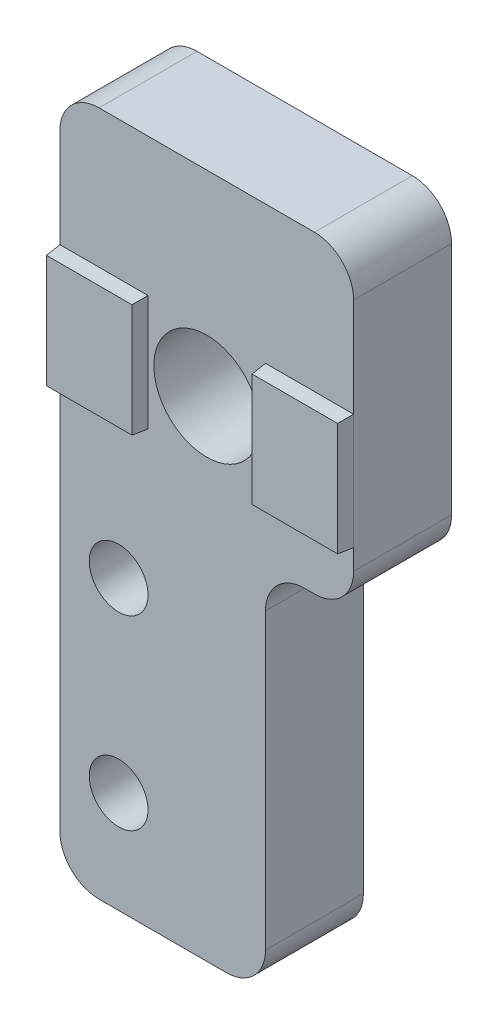
SolidWorks part; units mm, degrees
material "ABS"
ref_plane "Front Plane" through (0, 0, 0) normal (0, 0, 1) x (1, 0, 0)
ref_plane "Top Plane" through (0, 0, 0) normal (0, 1, 0) x (1, 0, 0)
ref_plane "Right Plane" through (0, 0, 0) normal (1, 0, 0) x (0, 0, -1)
sketch "Sketch1" plane through (0, 0, 0) normal (0, 0, 1) x (1, 0, 0)
  line L0 (0, -2) -> (0, -33)
  line L1 (2, 0) -> (13, 0)
  line L2 (2, -35) -> (8.5, -35)
  line L3 (15, -2) -> (15, -14)
  line L6 (7.5, 20) -> (7.5, -35) construction
  line L10 (13, -16) -> (12.5, -16)
  line L11 (10.5, -33) -> (10.5, -18)
  circle A0 centre (7.5, -10) radius 2.7
  circle A1 centre (3, -29.8) radius 1.5
  circle A2 centre (3, -20.3) radius 1.5
  arc A3 (10.5, -33) -> (8.5, -35) centre (8.5, -33) cw
  arc A4 (2, -35) -> (0, -33) centre (2, -33) cw
  arc A5 (0, -2) -> (2, 0) centre (2, -2) cw
  arc A6 (13, 0) -> (15, -2) centre (13, -2) cw
  arc A7 (15, -14) -> (13, -16) centre (13, -14) cw
  arc A8 (12.5, -16) -> (10.5, -18) centre (12.5, -18) ccw
  point P1 (0, 0)
  point P20 (0, -35)
  point P23 (0, 0)
  point P26 (15, 0)
  dimension "D3" = 5.4
  dimension "D4" = 10
  dimension "D5" = 9.5
  dimension "D6" = 5.2
  dimension "D7" = 3
  dimension "D8" = 3
  dimension "D12" = 2
  dimension "D1" = 15
  dimension "D2" = 35
  dimension "D9" = 10.5
  dimension "D10" = 16
  dimension "D11" = 7.5
extrude "Boss-Extrude1" add sketch "Sketch1" along normal blind 5
sketch "Sketch2" plane through (0, 0, 5) normal (0, 0, 1) x (1, 0, 0)
  line L0 (0, -2) -> (0, -33) construction
  line L1 (0, -7.05) -> (4.5, -7.05)
  line L2 (0, -7.05) -> (0, -12.95)
  line L3 (0, -12.95) -> (4.5, -12.95)
  line L4 (4.5, -7.05) -> (4.5, -12.95)
  line L5 (7.5, 0) -> (7.5, -35) construction
  line L6 (13, 0) -> (2, 0) construction
  line L8 (0, -10) -> (15, -10) construction
  line L9 (15, -14) -> (15, -2) construction
  line L10 (15, -12.95) -> (10.5, -12.95)
  line L11 (15, -7.05) -> (15, -12.95)
  line L12 (15, -7.05) -> (10.5, -7.05)
  line L13 (10.5, -7.05) -> (10.5, -12.95)
  line L14 (2, -35) -> (8.5, -35) construction
  point P10 (7.5, 0)
  dimension "D1" = 10
  dimension "D2" = 5.9
  dimension "D3" = 4.5
extrude "Boss-Extrude2" add sketch "Sketch2" along normal blind 0.75 draft 5
